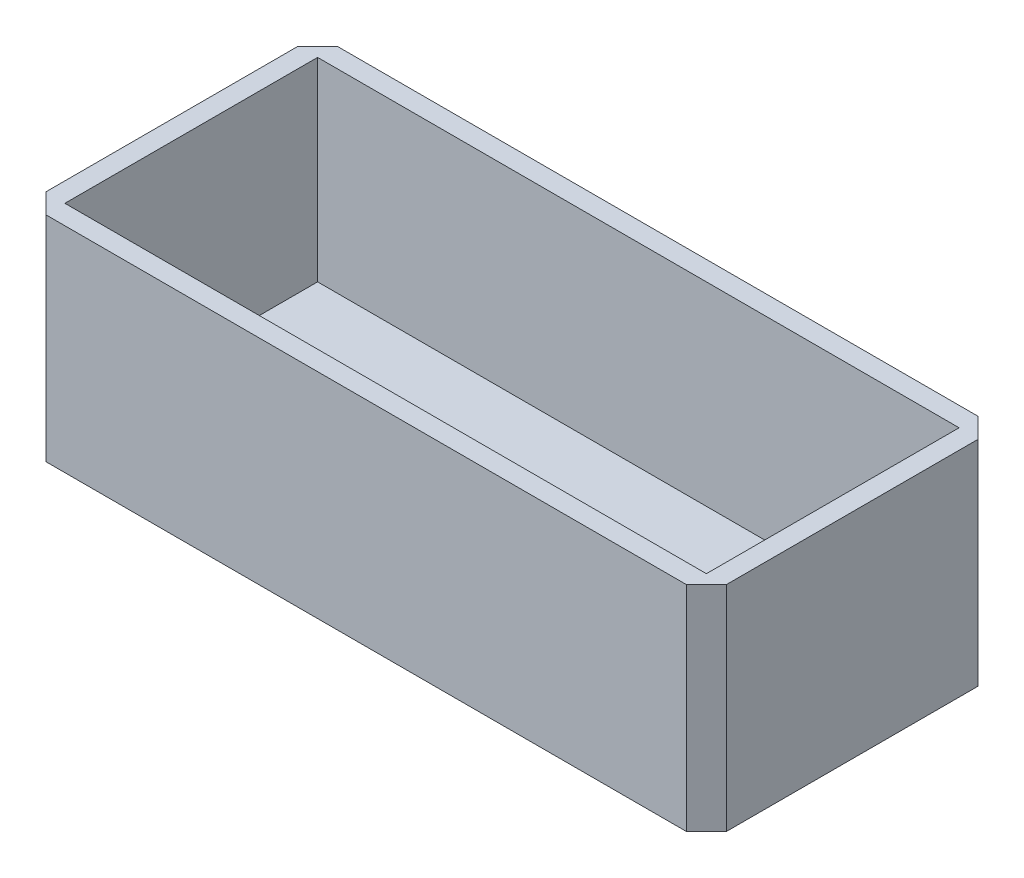
SolidWorks part; units mm, degrees
ref_plane "Alzado" through (0, 0, 0) normal (0, 0, 1) x (1, 0, 0)
ref_plane "Planta" through (0, 0, 0) normal (0, 1, 0) x (1, 0, 0)
ref_plane "Vista lateral" through (0, 0, 0) normal (1, 0, 0) x (0, 0, -1)
sketch "Croquis1" plane through (0, 0, 0) normal (0, 1, 0) x (1, 0, 0)
  line L1 (0, 0) -> (70, 0)
  line L2 (0, 0) -> (0, 30)
  line L3 (0, 30) -> (70, 30)
  line L4 (70, 0) -> (70, 30)
  dimension "D1" = 30
  dimension "D2" = 70
extrude "Saliente-Extruir1" add sketch "Croquis1" along normal blind 22
shell "Vaciado1" thickness 2
sketch "Croquis2" plane through (0, 2, 0) normal (0, 1, 0) x (1, 0, 0)
  line L0 (60, 15) -> (50, 15) construction
  line L4 (60, 17) -> (50, 17)
  line L5 (10, 15) -> (20, 15) construction
  line L6 (10, 17) -> (20, 17)
  line L7 (10, 13) -> (20, 13)
  line L8 (60, 13) -> (50, 13)
  arc A0 (10, 17) -> (10, 13) centre (10, 15) ccw
  arc A1 (20, 13) -> (20, 17) centre (20, 15) ccw
  arc A2 (60, 17) -> (60, 13) centre (60, 15) cw
  arc A3 (50, 13) -> (50, 17) centre (50, 15) cw
  point P7 (15, 15)
  point P11 (55, 15)
extrude "Cortar-Extruir1" cut sketch "Croquis2" against normal blind 22
sketch "Croquis3" plane through (0, 22, 0) normal (0, 1, 0) x (1, 0, 0)
  line L0 (0, 30) -> (2.0569, 30)
  line L1 (70, 30) -> (0, 30) construction
  line L2 (0, 30) -> (0, 27.9431)
  line L3 (0, 30) -> (0, 0) construction
  line L4 (0, 27.9431) -> (2.0569, 30)
  line L9 (70, 30) -> (70, 27.9431)
  line L10 (70, 30) -> (67.9431, 30)
  line L11 (70, 27.9431) -> (67.9431, 30)
  line L12 (70, 0) -> (67.9431, 0)
  line L13 (70, 2.0569) -> (67.9431, 0)
  line L14 (70, 0) -> (70, 2.0569)
  line L15 (0, 0) -> (0, 2.0569)
  line L16 (0, 0) -> (2.0569, 0)
  line L17 (0, 2.0569) -> (2.0569, 0)
  line M22 (0, 30) -> (0, 0)
  line M23 (0, 0) -> (70, 0)
  line M24 (70, 0) -> (70, 30)
  line M25 (70, 30) -> (0, 30)
extrude "Cortar-Extruir3" cut sketch "Croquis3" against normal blind 22 contours L17 M22 M23 | L13 M24 M23 | L11 M24 M25 | L0 L4 L2
